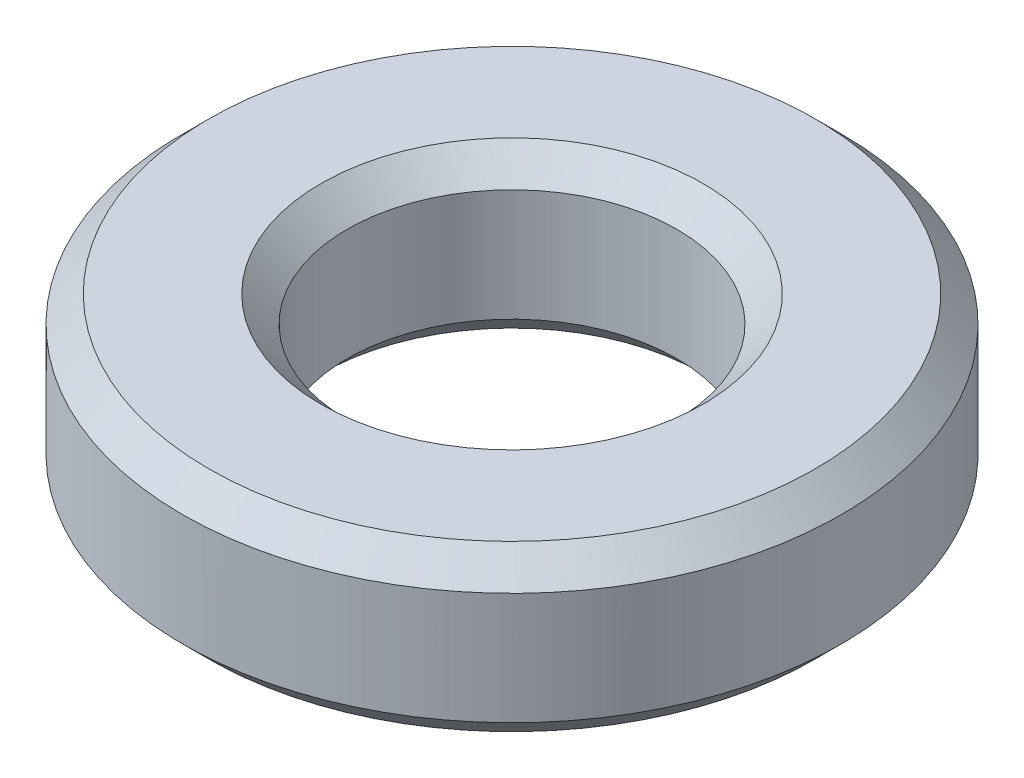
SolidWorks part; units mm, degrees
ref_plane "Front Plane" through (0, 0, 0) normal (0, 0, 1) x (1, 0, 0)
ref_plane "Top Plane" through (0, 0, 0) normal (0, 1, 0) x (1, 0, 0)
ref_plane "Right Plane" through (0, 0, 0) normal (1, 0, 0) x (0, 0, -1)
sketch "Sketch1" plane through (0, 0, 0) normal (0, 0, 1) x (1, 0, 0)
  line L0 (0, 0) -> (0, 1.3501) construction
  line L1 (1.5875, 0.7938) -> (3.175, 0.7938)
  line L2 (3.175, 0.7938) -> (3.175, -0.7938)
  line L3 (3.175, -0.7938) -> (1.5875, -0.7938)
  line L4 (1.5875, -0.7938) -> (1.5875, 0.7938)
  point P6 (1.5875, 0)
  dimension "D1" = 3.175
  dimension "D2" = 6.35
  dimension "D3" = 1.5875
revolve "Revolve1" add sketch "Sketch1" angle 360 about L0
chamfer "Chamfer1" distance 0.254 angle 45 4 edges at (0, -0.7938, -3.175) (0, 0.7938, -3.175) (0, 0.7938, -1.5875) (0, -0.7938, -1.5875)
